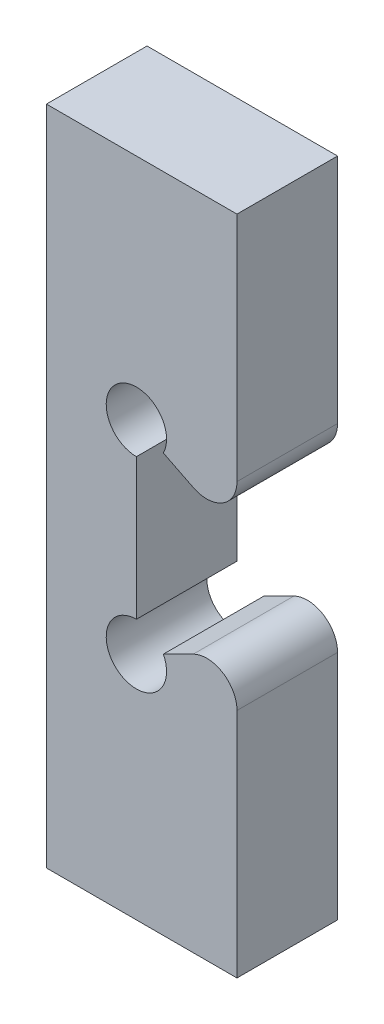
SolidWorks part; units mm, degrees
ref_plane "Alzado" through (0, 0, 0) normal (0, 0, 1) x (1, 0, 0)
ref_plane "Planta" through (0, 0, 0) normal (0, 1, 0) x (1, 0, 0)
ref_plane "Vista lateral" through (0, 0, 0) normal (1, 0, 0) x (0, 0, -1)
sketch "Croquis1" plane through (0, 0, 0) normal (0, 0, 1) x (1, 0, 0)
  line L15 (-64, 25.6) -> (-73.4712, 25.6)
  line L16 (-73.4712, 25.6) -> (-73.4712, -7.2848)
  line L17 (-73.4712, -7.2848) -> (-64, -7.2848)
  line L20 (-64, 6.6576) -> (-64, -7.2848)
  line L21 (-64, 25.6) -> (-64, 11.6576)
  line L22 (-69, 4.1576) -> (-64, 6.6576)
  line L23 (-64, 11.6576) -> (-69, 14.1576)
  line L24 (-69, 14.1576) -> (-69, 4.1576)
  line L25 (-64, 4.2306) -> (-64, -7.2848)
  line L26 (-64, 25.6) -> (-64, 14.0847)
  line L27 (-67.6584, 4.8284) -> (-66.1708, 5.5722)
  line L28 (-66.1708, 12.743) -> (-67.6584, 13.4868)
  line L29 (-69, 12.6576) -> (-69, 5.6576)
  arc A0 (-67.6584, 13.4868) -> (-69, 12.6576) centre (-69, 14.1576) ccw
  arc A1 (-69, 5.6576) -> (-67.6584, 4.8284) centre (-69, 4.1576) ccw
  arc A2 (-64, 4.2306) -> (-66.1708, 5.5722) centre (-65.5, 4.2306) ccw
  arc A3 (-64, 14.0847) -> (-66.1708, 12.743) centre (-65.5, 14.0847) cw
  dimension "D2" = 1.5
  dimension "D1" = 0
extrude "Saliente-Extruir1" add sketch "Croquis1" against normal up to surface (5 mm away)
